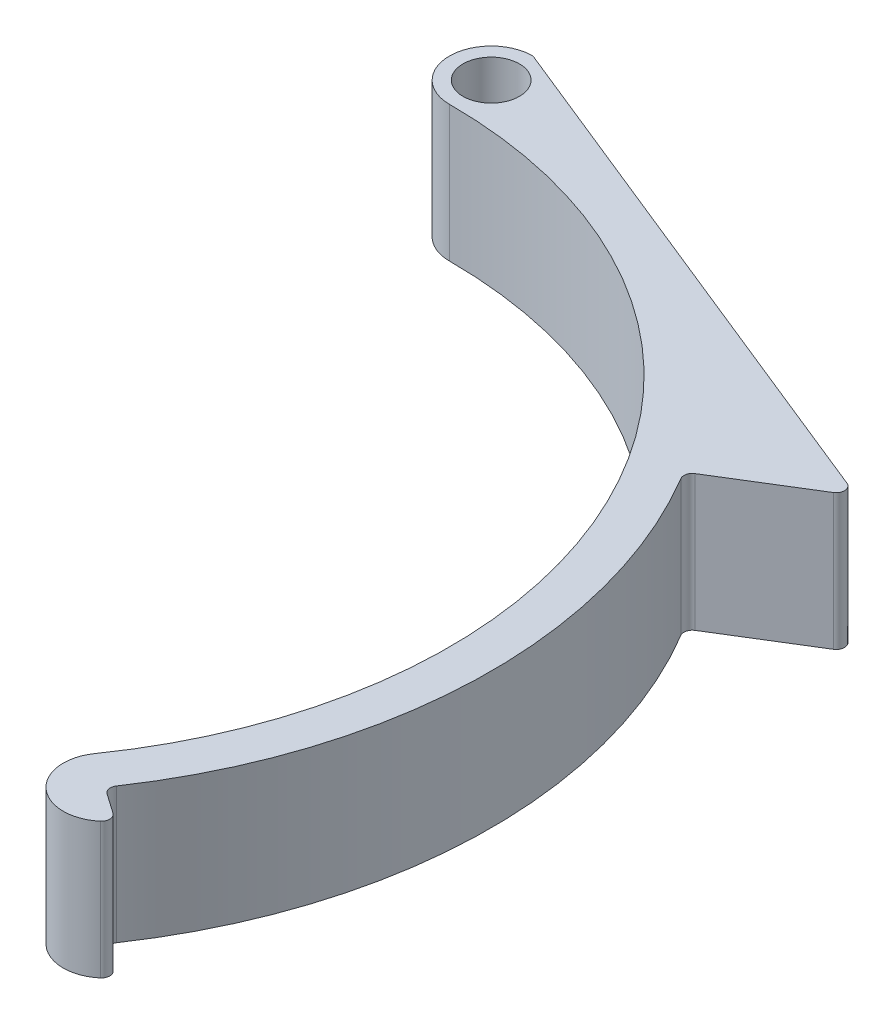
SolidWorks part; units mm, degrees
ref_plane "Front Plane" through (0, 0, 0) normal (0, 0, 1) x (1, 0, 0)
ref_plane "Top Plane" through (0, 0, 0) normal (0, 1, 0) x (1, 0, 0)
ref_plane "Right Plane" through (0, 0, 0) normal (1, 0, 0) x (0, 0, -1)
sketch "Sketch1" plane through (0, 0, 0) normal (0, 1, 0) x (1, 0, 0)
  line L0 (0, 0) -> (36.8618, -25.8109) construction
  line L1 (0, 0) -> (0, -45) construction
  line L2 (0, 0) -> (67.9838, -47.6027) construction
  line L3 (0, 53) -> (51.921, 32.0189)
  line L4 (51.921, 32.0189) -> (41.707, 25.7201)
  line L5 (0, 53) -> (0, 49)
  line L6 (40.1385, -28.1052) -> (43.4151, -30.3996)
  line L7 (0, 49) -> (0, 53)
  circle A0 centre (0, 0) radius 45 construction
  arc A1 (0, 45) -> (36.8618, -25.8109) centre (0, 0) cw
  arc A2 (0, 45) -> (0, 53) centre (0, 49) cw
  arc A3 (36.8618, -25.8109) -> (43.4151, -30.3996) centre (40.1385, -28.1052) ccw
  arc A4 (40.1385, -28.1052) -> (0, 49) centre (0, 0) ccw
  circle A5 centre (0, 49) radius 2.7
  arc A6 (41.707, 25.7201) -> (0, 49) centre (0, 0) ccw
  dimension "D1" = 90
  dimension "D5" = 56
  dimension "D6" = 5.4
  dimension "D2" = 55
  dimension "D3" = 8
  dimension "D4" = 4
  dimension "D7" = 12
extrude "Boss-Extrude1" add sketch "Sketch1" along normal blind 13 contours A5 L5 A2 A1 A3 L6 A4 | A5 A4 L4 L3 L5
fillet "Fillet1" radius 0.8 5 edges at (0, 6.5, -53) (40.1385, 6.5, 28.1052) (43.4151, 6.5, 30.3996) (51.921, 6.5, -32.0189) (41.707, 6.5, -25.7201)
